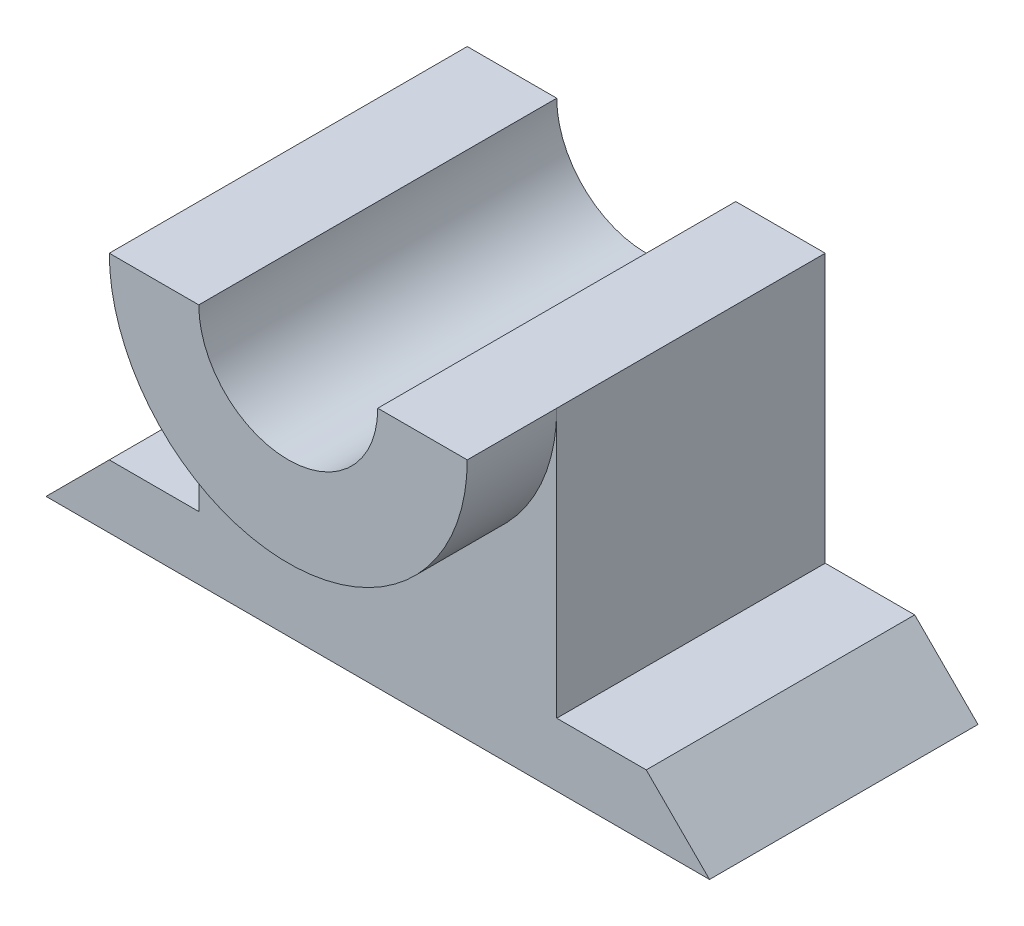
SolidWorks part; units mm, degrees
ref_plane "Front Plane" through (0, 0, 0) normal (0, 0, 1) x (1, 0, 0)
ref_plane "Top Plane" through (0, 0, 0) normal (0, 1, 0) x (1, 0, 0)
ref_plane "Right Plane" through (0, 0, 0) normal (1, 0, 0) x (0, 0, -1)
sketch "Sketch1" plane through (0, 0, 0) normal (0, 0, 1) x (1, 0, 0)
  line L0 (0, 0) -> (-10, 0)
  line L2 (0, 0) -> (0, 30)
  line L3 (0, 30) -> (40, 30)
  line L4 (40, 0) -> (40, 30)
  line L5 (-10, 0) -> (-17.0711, -7.0711)
  line L6 (-17.0711, -7.0711) -> (57.0711, -7.0711)
  line L7 (57.0711, -7.0711) -> (50, 0)
  line L8 (50, 0) -> (40, 0)
  dimension "D1" = 40
  dimension "D2" = 30
  dimension "D3" = 10
  dimension "D4" = 10
  dimension "D5" = 45
  dimension "D6" = 10
  dimension "D7" = 10
  dimension "D8" = 45
sketch "Sketch2" plane through (0, 0, 0) normal (0, 0, 1) x (1, 0, 0)
extrude "Boss-Extrude1" add sketch "Sketch1" along normal blind 30
sketch "Sketch3" plane through (0, 0, 0) normal (0, 0, 1) x (1, 0, 0)
  line L0 (40, 30) -> (0, 30) construction
  line L1 (0, 30) -> (0, 0) construction
  line L2 (40, 0) -> (40, 30) construction
  line L3 (0, 30) -> (40, 30)
  arc A0 (0, 30) -> (40, 30) centre (20, 30) ccw
extrude "Boss-Extrude2" add sketch "Sketch3" along normal blind 40
sketch "Sketch4" plane through (0, 0, 40) normal (0, 0, 1) x (1, 0, 0)
  line L0 (40, 30) -> (0, 30) construction
  line L1 (10, 30) -> (30, 30)
  arc A0 (10, 30) -> (30, 30) centre (20, 30) ccw
  dimension "D1" = 10
extrude "Cut-Extrude1" cut sketch "Sketch4" against normal blind 40
